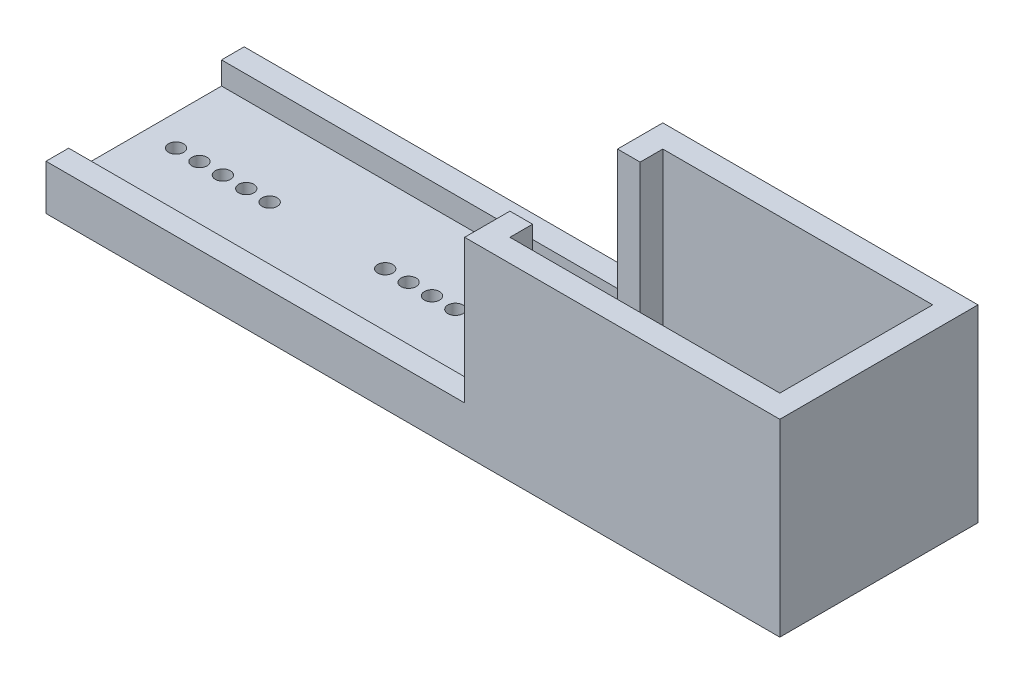
SolidWorks part; units mm, degrees
ref_plane "Front Plane" through (0, 0, 0) normal (0, 0, 1) x (1, 0, 0)
ref_plane "Top Plane" through (0, 0, 0) normal (0, 1, 0) x (1, 0, 0)
ref_plane "Right Plane" through (0, 0, 0) normal (1, 0, 0) x (0, 0, -1)
sketch "Sketch1" plane through (0, 0, 0) normal (0, 1, 0) x (1, 0, 0)
  line L1 (-48.6, -13.125) -> (48.6, -13.125)
  line L2 (-48.6, -13.125) -> (-48.6, 13.125)
  line L3 (-48.6, 13.125) -> (48.6, 13.125)
  line L4 (48.6, -13.125) -> (48.6, 13.125)
  line L5 (-48.6, -13.125) -> (48.6, 13.125) construction
  line L6 (-48.6, 13.125) -> (48.6, -13.125) construction
  point P0 (0, 0)
  dimension "D1" = 26.25
  dimension "D2" = 97.2
extrude "Boss-Extrude1" add sketch "Sketch1" along normal blind 3
sketch "Sketch2" plane through (0, 3, 0) normal (0, 1, 0) x (1, 0, 0)
  line L0 (48.6, 13.125) -> (-48.6, 13.125) construction
  line L1 (48.6, -13.125) -> (9.85, -13.125)
  line L2 (48.6, -13.125) -> (48.6, 13.125)
  line L3 (48.6, 13.125) -> (45.6, 13.125)
  line L5 (45.6, 13.125) -> (9.6, 13.125)
  line L6 (45.6, 10.125) -> (9.85, 10.125)
  line L12 (45.6, -10.125) -> (9.85, -10.125)
  line L15 (45.6, -10.125) -> (45.6, 10.125)
  line L16 (9.85, 10.125) -> (9.85, 7.125)
  line L17 (9.85, 7.125) -> (6.85, 7.125)
  line L18 (6.85, 7.125) -> (6.85, 13.125)
  line L19 (9.85, -10.125) -> (9.85, -7.125)
  line L20 (9.85, -7.125) -> (6.85, -7.125)
  line L21 (6.85, -7.125) -> (6.85, -13.125)
  line L22 (-48.6, -13.125) -> (48.6, -13.125) construction
  line L23 (6.85, 13.125) -> (9.6, 13.125)
  line L24 (9.85, -13.125) -> (6.85, -13.125)
  dimension "D1" = 3
  dimension "D2" = 35.75
  dimension "D3" = 3
  dimension "D4" = 3
  dimension "D5" = 3
  dimension "D6" = 3
  dimension "D7" = 3
extrude "Boss-Extrude2" add sketch "Sketch2" along normal blind 22
sketch "Sketch3" plane through (0, 3, 0) normal (0, 1, 0) x (1, 0, 0)
  line L0 (9.85, 10.125) -> (45.6, 10.125) construction
  line L1 (14.35, 10.125) -> (20.85, 10.125)
  line L2 (14.35, 10.125) -> (14.35, -10.125)
  line L3 (14.35, -10.125) -> (20.85, -10.125)
  line L4 (20.85, 10.125) -> (20.85, -10.125)
  line L5 (45.6, -10.125) -> (9.85, -10.125) construction
  line L7 (9.85, 7.125) -> (9.85, 10.125) construction
  dimension "D1" = 6.5
  dimension "D2" = 11
extrude "Cut-Extrude1" cut sketch "Sketch3" against normal through all
sketch "Sketch4" plane through (0, 3, 0) normal (0, 1, 0) x (1, 0, 0)
  line L0 (-24.45, 13.125) -> (-24.45, -13.125)
  line L1 (6.85, 13.125) -> (-48.6, 13.125) construction
  line L2 (-48.6, -13.125) -> (6.85, -13.125) construction
  line L3 (45.6, 10.125) -> (45.6, -10.125) construction
  dimension "D1" = 70.05
sketch "Sketch5" plane through (0, 3, 0) normal (0, 1, 0) x (1, 0, 0)
  line L0 (-48.6, 0) -> (45.6, 0) construction
  line L1 (-48.6, 13.125) -> (-48.6, -13.125) construction
  line L2 (45.6, 10.125) -> (45.6, -10.125) construction
  line L3 (-16.8, 0) -> (-24.45, 0) construction
  line L5 (-24.45, 13.125) -> (-24.45, -13.125) construction
  line L6 (-24.45, 13.125) -> (-24.45, -13.125) construction
  line L7 (-24.45, 0) -> (-32.1, 0) construction
  circle A0 centre (-32.1, 0) radius 1
  circle A1 centre (-16.8, 0) radius 1
  circle A2 centre (-13.7, 0) radius 1
  circle A3 centre (-10.6, 0) radius 1
  circle A4 centre (-7.5, 0) radius 1
  circle A5 centre (-4.4, 0) radius 1
  circle A6 centre (-35.2, 0) radius 1
  circle A7 centre (-38.3, 0) radius 1
  circle A8 centre (-41.4, 0) radius 1
  circle A9 centre (-44.5, 0) radius 1
  dimension "D1" = 5
  dimension "D2" = 2
  dimension "D4" = 15.3
  dimension "D3" = 5
extrude "Cut-Extrude2" cut sketch "Sketch5" against normal through all
fillet "Fillet1" [suppressed] radius 10
sketch "Sketch6" plane through (0, 3, 0) normal (0, 1, 0) x (1, 0, 0)
  line L0 (6.85, 13.125) -> (6.85, 7.125) construction
  line L1 (-48.6, 13.125) -> (6.85, 13.125)
  line L2 (-48.6, 13.125) -> (-48.6, 10.125)
  line L3 (-48.6, 10.125) -> (6.85, 10.125)
  line L4 (6.85, 13.125) -> (6.85, 10.125)
  line L5 (6.85, -7.125) -> (6.85, -13.125) construction
  line L6 (-48.6, -13.125) -> (6.85, -13.125)
  line L7 (-48.6, -13.125) -> (-48.6, -10.125)
  line L8 (-48.6, -10.125) -> (6.85, -10.125)
  line L9 (6.85, -13.125) -> (6.85, -10.125)
  line L10 (20.85, 10.125) -> (45.6, 10.125) construction
  line L13 (45.6, -10.125) -> (20.85, -10.125) construction
extrude "Boss-Extrude3" add sketch "Sketch6" along normal blind 3
